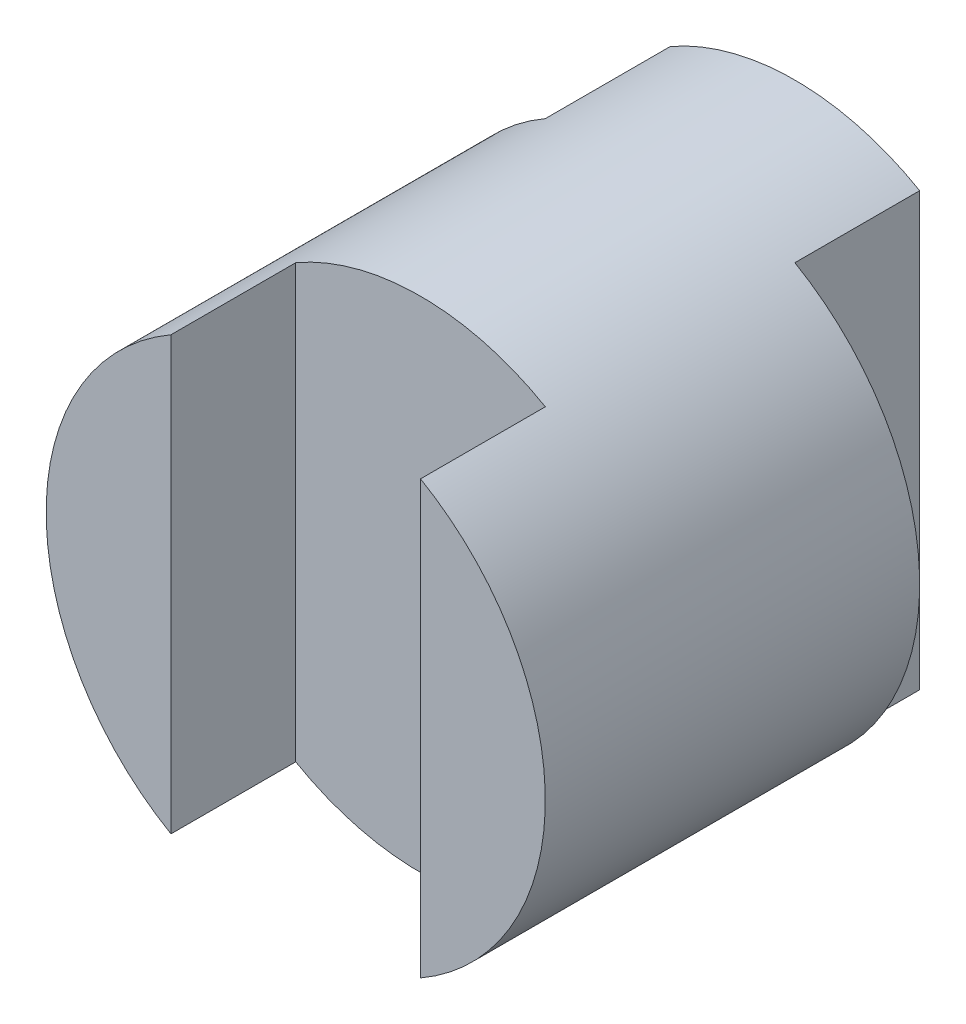
SolidWorks part; units mm, degrees
ref_plane "Front" through (0, 0, 0) normal (0, 0, 1) x (1, 0, 0)
ref_plane "Top" through (0, 0, 0) normal (0, 1, 0) x (1, 0, 0)
ref_plane "Right" through (0, 0, 0) normal (1, 0, 0) x (0, 0, -1)
sketch "Sketch1" plane through (0, 0, 0) normal (0, 0, 1) x (1, 0, 0)
  circle A0 centre (0, 0) radius 2
  dimension "D1" = 4
extrude "Boss-Extrude1" add sketch "Sketch1" along normal blind 4
sketch "Sketch2" plane through (0, 0, 0) normal (0, 1, 0) x (1, 0, 0)
  line L7 (-2.3139, -1) -> (-1, -1)
  line L8 (-1, -1) -> (-1, 0.234)
  line L9 (-1, 0.234) -> (-2.5868, 0.1999)
  line L15 (-2, 0) -> (-2, -4) construction
  line L16 (2, 0) -> (-2, 0) construction
  line L17 (-2.5868, 0.1999) -> (-2.3139, -1)
  line L18 (-1, -3) -> (-1, -4)
  line L19 (-2, -4) -> (2, -4) construction
  line L20 (-1, -4) -> (1, -4)
  line L21 (1, -4) -> (1, -3)
  line L22 (1, -3) -> (-1, -3)
  dimension "D1" = 2
  dimension "D2" = 1
  dimension "D5" = 1
  dimension "D6" = 1
extrude "Cut-Extrude1" cut sketch "Sketch2" against normal mid plane 10
sketch "Sketch3" plane through (0, 0, 0) normal (0, 1, 0) x (1, 0, 0)
  line L1 (2, 0) -> (1, 0)
  line L2 (2, 0) -> (2, -1)
  line L3 (2, -1) -> (1, -1)
  line L4 (1, 0) -> (1, -1)
  dimension "D1" = 1
  dimension "D2" = 1
extrude "Cut-Extrude2" cut sketch "Sketch3" against normal mid plane 10
